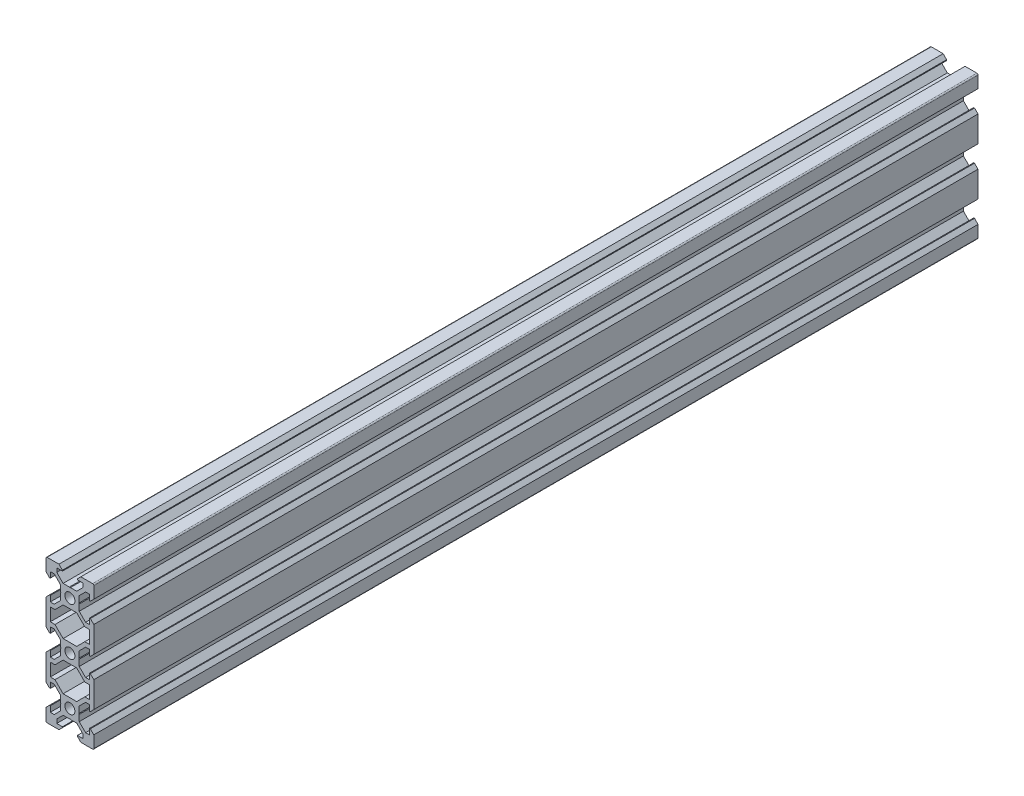
SolidWorks part; units mm, degrees
material "6061-T6 (SS)"
ref_plane "Front Plane" through (0, 0, 0) normal (0, 0, 1) x (1, 0, 0)
ref_plane "Top Plane" through (0, 0, 0) normal (0, 1, 0) x (1, 0, 0)
ref_plane "Right Plane" through (0, 0, 0) normal (1, 0, 0) x (0, 0, -1)
sketch "Sketch1" plane through (0, 0, 0) normal (0, 0, 1) x (1, 0, 0)
  line L0 (0, 0) -> (10, 0) construction
  line L1 (9.5, -30) -> (-9.5, -30)
  line L2 (10, -29.5) -> (10, 29.5)
  line L3 (9.5, 30) -> (-9.5, 30)
  line L4 (-10, -29.5) -> (-10, 29.5)
  line L5 (10, -30) -> (-10, 30) construction
  line L6 (10, 30) -> (-10, -30) construction
  circle A0 centre (0, 20) radius 2.1
  circle A1 centre (0, 0) radius 2.1
  circle A2 centre (0, -20) radius 2.1
  arc A3 (-9.5, -30) -> (-10, -29.5) centre (-9.5, -29.5) cw
  arc A4 (9.5, -30) -> (10, -29.5) centre (9.5, -29.5) ccw
  arc A5 (10, 29.5) -> (9.5, 30) centre (9.5, 29.5) ccw
  arc A6 (-9.5, 30) -> (-10, 29.5) centre (-9.5, 29.5) ccw
  point P0 (0, 0)
  line B0 (0, 20) -> (0, 30) construction
  line B1 (0, 23.69) -> (-0.21, 23.9)
  line B2 (-0.21, 23.9) -> (-2.8393, 23.9)
  line B3 (-2.8393, 23.9) -> (-5.5, 26.5607)
  line B4 (-5.5, 26.5607) -> (-5.5, 28.2)
  line B5 (-5.5, 28.2) -> (-3.125, 28.2)
  line B6 (-3.125, 28.2) -> (-3.125, 28.545)
  line B7 (-3.125, 28.545) -> (-4.58, 30)
  line B8 (-4.58, 30) -> (4.58, 30)
  line B9 (0, 20) -> (-5.9132, 25.9132) construction
  line B10 (3.125, 28.545) -> (4.58, 30)
  line B11 (3.125, 28.2) -> (3.125, 28.545)
  line B12 (5.5, 28.2) -> (3.125, 28.2)
  line B13 (5.5, 26.5607) -> (5.5, 28.2)
  line B14 (2.8393, 23.9) -> (5.5, 26.5607)
  line B15 (0.21, 23.9) -> (2.8393, 23.9)
  line B16 (0, 23.69) -> (0.21, 23.9)
  line B17 (0, 20) -> (-10, 20) construction
  line B18 (-3.69, 20) -> (-3.9, 19.79)
  line B19 (-3.9, 19.79) -> (-3.9, 17.1607)
  line B20 (-3.9, 17.1607) -> (-6.5607, 14.5)
  line B21 (-6.5607, 14.5) -> (-8.2, 14.5)
  line B22 (-8.2, 14.5) -> (-8.2, 16.875)
  line B23 (-8.2, 16.875) -> (-8.545, 16.875)
  line B24 (-8.545, 16.875) -> (-10, 15.42)
  line B25 (-10, 15.42) -> (-10, 24.58)
  line B26 (0, 20) -> (-5.9132, 14.0868) construction
  line B27 (-8.545, 23.125) -> (-10, 24.58)
  line B28 (-8.2, 23.125) -> (-8.545, 23.125)
  line B29 (-8.2, 25.5) -> (-8.2, 23.125)
  line B30 (-6.5607, 25.5) -> (-8.2, 25.5)
  line B31 (-3.9, 22.8393) -> (-6.5607, 25.5)
  line B32 (-3.9, 20.21) -> (-3.9, 22.8393)
  line B33 (-3.69, 20) -> (-3.9, 20.21)
  line B34 (0, 0) -> (-10, 0) construction
  line B35 (-3.69, 0) -> (-3.9, -0.21)
  line B36 (-3.9, -0.21) -> (-3.9, -2.8393)
  line B37 (-3.9, -2.8393) -> (-6.5607, -5.5)
  line B38 (-6.5607, -5.5) -> (-8.2, -5.5)
  line B39 (-8.2, -5.5) -> (-8.2, -3.125)
  line B40 (-8.2, -3.125) -> (-8.545, -3.125)
  line B41 (-8.545, -3.125) -> (-10, -4.58)
  line B42 (-10, -4.58) -> (-10, 4.58)
  line B43 (0, 0) -> (-5.9132, -5.9132) construction
  line B44 (-8.545, 3.125) -> (-10, 4.58)
  line B45 (-8.2, 3.125) -> (-8.545, 3.125)
  line B46 (-8.2, 5.5) -> (-8.2, 3.125)
  line B47 (-6.5607, 5.5) -> (-8.2, 5.5)
  line B48 (-3.9, 2.8393) -> (-6.5607, 5.5)
  line B49 (-3.9, 0.21) -> (-3.9, 2.8393)
  line B50 (-3.69, 0) -> (-3.9, 0.21)
  line B51 (0, -20) -> (-10, -20) construction
  line B52 (-3.69, -20) -> (-3.9, -20.21)
  line B53 (-3.9, -20.21) -> (-3.9, -22.8393)
  line B54 (-3.9, -22.8393) -> (-6.5607, -25.5)
  line B55 (-6.5607, -25.5) -> (-8.2, -25.5)
  line B56 (-8.2, -25.5) -> (-8.2, -23.125)
  line B57 (-8.2, -23.125) -> (-8.545, -23.125)
  line B58 (-8.545, -23.125) -> (-10, -24.58)
  line B59 (-10, -24.58) -> (-10, -15.42)
  line B60 (0, -20) -> (-5.9132, -25.9132) construction
  line B61 (-8.545, -16.875) -> (-10, -15.42)
  line B62 (-8.2, -16.875) -> (-8.545, -16.875)
  line B63 (-8.2, -14.5) -> (-8.2, -16.875)
  line B64 (-6.5607, -14.5) -> (-8.2, -14.5)
  line B65 (-3.9, -17.1607) -> (-6.5607, -14.5)
  line B66 (-3.9, -19.79) -> (-3.9, -17.1607)
  line B67 (-3.69, -20) -> (-3.9, -19.79)
  line B68 (0, -20) -> (0, -30) construction
  line B69 (0, -23.69) -> (0.21, -23.9)
  line B70 (0.21, -23.9) -> (2.8393, -23.9)
  line B71 (2.8393, -23.9) -> (5.5, -26.5607)
  line B72 (5.5, -26.5607) -> (5.5, -28.2)
  line B73 (5.5, -28.2) -> (3.125, -28.2)
  line B74 (3.125, -28.2) -> (3.125, -28.545)
  line B75 (3.125, -28.545) -> (4.58, -30)
  line B76 (4.58, -30) -> (-4.58, -30)
  line B77 (0, -20) -> (5.9132, -25.9132) construction
  line B78 (-3.125, -28.545) -> (-4.58, -30)
  line B79 (-3.125, -28.2) -> (-3.125, -28.545)
  line B80 (-5.5, -28.2) -> (-3.125, -28.2)
  line B81 (-5.5, -26.5607) -> (-5.5, -28.2)
  line B82 (-2.8393, -23.9) -> (-5.5, -26.5607)
  line B83 (-0.21, -23.9) -> (-2.8393, -23.9)
  line B84 (0, -23.69) -> (-0.21, -23.9)
  line B85 (0, -20) -> (10, -20) construction
  line B86 (3.69, -20) -> (3.9, -19.79)
  line B87 (3.9, -19.79) -> (3.9, -17.1607)
  line B88 (3.9, -17.1607) -> (6.5607, -14.5)
  line B89 (6.5607, -14.5) -> (8.2, -14.5)
  line B90 (8.2, -14.5) -> (8.2, -16.875)
  line B91 (8.2, -16.875) -> (8.545, -16.875)
  line B92 (8.545, -16.875) -> (10, -15.42)
  line B93 (10, -15.42) -> (10, -24.58)
  line B94 (0, -20) -> (5.9132, -14.0868) construction
  line B95 (8.545, -23.125) -> (10, -24.58)
  line B96 (8.2, -23.125) -> (8.545, -23.125)
  line B97 (8.2, -25.5) -> (8.2, -23.125)
  line B98 (6.5607, -25.5) -> (8.2, -25.5)
  line B99 (3.9, -22.8393) -> (6.5607, -25.5)
  line B100 (3.9, -20.21) -> (3.9, -22.8393)
  line B101 (3.69, -20) -> (3.9, -20.21)
  line B102 (0, 0) -> (10, 0) construction
  line B103 (3.69, 0) -> (3.9, 0.21)
  line B104 (3.9, 0.21) -> (3.9, 2.8393)
  line B105 (3.9, 2.8393) -> (6.5607, 5.5)
  line B106 (6.5607, 5.5) -> (8.2, 5.5)
  line B107 (8.2, 5.5) -> (8.2, 3.125)
  line B108 (8.2, 3.125) -> (8.545, 3.125)
  line B109 (8.545, 3.125) -> (10, 4.58)
  line B110 (10, 4.58) -> (10, -4.58)
  line B111 (0, 0) -> (5.9132, 5.9132) construction
  line B112 (8.545, -3.125) -> (10, -4.58)
  line B113 (8.2, -3.125) -> (8.545, -3.125)
  line B114 (8.2, -5.5) -> (8.2, -3.125)
  line B115 (6.5607, -5.5) -> (8.2, -5.5)
  line B116 (3.9, -2.8393) -> (6.5607, -5.5)
  line B117 (3.9, -0.21) -> (3.9, -2.8393)
  line B118 (3.69, 0) -> (3.9, -0.21)
  line B119 (0, 20) -> (10, 20) construction
  line B120 (3.69, 20) -> (3.9, 20.21)
  line B121 (3.9, 20.21) -> (3.9, 22.8393)
  line B122 (3.9, 22.8393) -> (6.5607, 25.5)
  line B123 (6.5607, 25.5) -> (8.2, 25.5)
  line B124 (8.2, 25.5) -> (8.2, 23.125)
  line B125 (8.2, 23.125) -> (8.545, 23.125)
  line B126 (8.545, 23.125) -> (10, 24.58)
  line B127 (10, 24.58) -> (10, 15.42)
  line B128 (0, 20) -> (5.9132, 25.9132) construction
  line B129 (8.545, 16.875) -> (10, 15.42)
  line B130 (8.2, 16.875) -> (8.545, 16.875)
  line B131 (8.2, 14.5) -> (8.2, 16.875)
  line B132 (6.5607, 14.5) -> (8.2, 14.5)
  line B133 (3.9, 17.1607) -> (6.5607, 14.5)
  line B134 (3.9, 19.79) -> (3.9, 17.1607)
  line B135 (3.69, 20) -> (3.9, 19.79)
  line B136 (-8.2, 7.3) -> (-8.2, 12.7)
  line B137 (-8.2, 12.7) -> (-6.2393, 12.7)
  line B138 (-6.2393, 12.7) -> (-2.8393, 16.1)
  line B139 (-2.8393, 16.1) -> (2.8393, 16.1)
  line B140 (0, 16.1) -> (0, 10) construction
  line B141 (0, 10) -> (-8.2, 10) construction
  line B142 (6.2393, 12.7) -> (2.8393, 16.1)
  line B143 (8.2, 12.7) -> (6.2393, 12.7)
  line B144 (8.2, 7.3) -> (8.2, 12.7)
  line B145 (8.2, 7.3) -> (6.2393, 7.3)
  line B146 (6.2393, 7.3) -> (2.8393, 3.9)
  line B147 (-2.8393, 3.9) -> (2.8393, 3.9)
  line B148 (-6.2393, 7.3) -> (-2.8393, 3.9)
  line B149 (-8.2, 7.3) -> (-6.2393, 7.3)
  line B150 (0, 16.1) -> (0, 20) construction
  line B151 (0, 20) -> (-5.0927, 14.9073) construction
  line B152 (-8.2, -12.7) -> (-8.2, -7.3)
  line B153 (-8.2, -7.3) -> (-6.2393, -7.3)
  line B154 (-6.2393, -7.3) -> (-2.8393, -3.9)
  line B155 (-2.8393, -3.9) -> (2.8393, -3.9)
  line B156 (0, -3.9) -> (0, -10) construction
  line B157 (0, -10) -> (-8.2, -10) construction
  line B158 (6.2393, -7.3) -> (2.8393, -3.9)
  line B159 (8.2, -7.3) -> (6.2393, -7.3)
  line B160 (8.2, -12.7) -> (8.2, -7.3)
  line B161 (8.2, -12.7) -> (6.2393, -12.7)
  line B162 (6.2393, -12.7) -> (2.8393, -16.1)
  line B163 (-2.8393, -16.1) -> (2.8393, -16.1)
  line B164 (-6.2393, -12.7) -> (-2.8393, -16.1)
  line B165 (-8.2, -12.7) -> (-6.2393, -12.7)
  line B166 (0, -3.9) -> (0, 0) construction
  line B167 (0, 0) -> (-5.0927, -5.0927) construction
  dimension "D3" = 4.2
  dimension "D5" = 0.5
  dimension "D1" = 20
  dimension "D2" = 60
  dimension "D4" = 40
sketch_block_instance "V Slot 1-4"
sketch_block "V Slot 1" parameters "D1"=10, "D2"=11, "D3"=4.3, "D4"=1.8, "D5"=0.21, "D6"=45, "D7"=9.16, "D8"=1.5, "D9"=6.25
sketch_block_instance "V Slot 1-5"
sketch_block_instance "V Slot 1-6"
sketch_block_instance "V Slot 1-7"
sketch_block_instance "V Slot 1-8"
sketch_block_instance "V Slot 1-9"
sketch_block_instance "V Slot 1-10"
sketch_block_instance "V Slot 1-11"
sketch_block_instance "Center Cutout 1-1"
sketch_block "Center Cutout 1" parameters "D1"=5.4, "D2"=12.2, "D3"=8.2, "D4"=45, "D5"=10, "D6"=1.5
sketch_block_instance "Center Cutout 1-2"
extrude "Boss-Extrude1" add sketch "Sketch1" along normal blind 370 contours B135 B120 B121 B122 B123 B124 B125 B126 L2 A5 L3 B10 B11 B12 B13 B14 B15 B16 B1 B2 B3 B4 B5 B6 B7 A6 L4 B27 B28 B29 B30 B31 B32 B33 B18 B19 B20 B21 B22 B23 B24 B44 B45 B46 B47 B48 B49 B50 B35
ref_plane "Plane1" through (0, 20, 0) normal (0, 1, 0) x (1, 0, 0)
ref_plane "Plane2" through (0, 0, 0) normal (0, -1, 0) x (-1, 0, 0)
ref_plane "Plane3" through (0, -20, 0) normal (0, -1, 0) x (-1, 0, 0)
